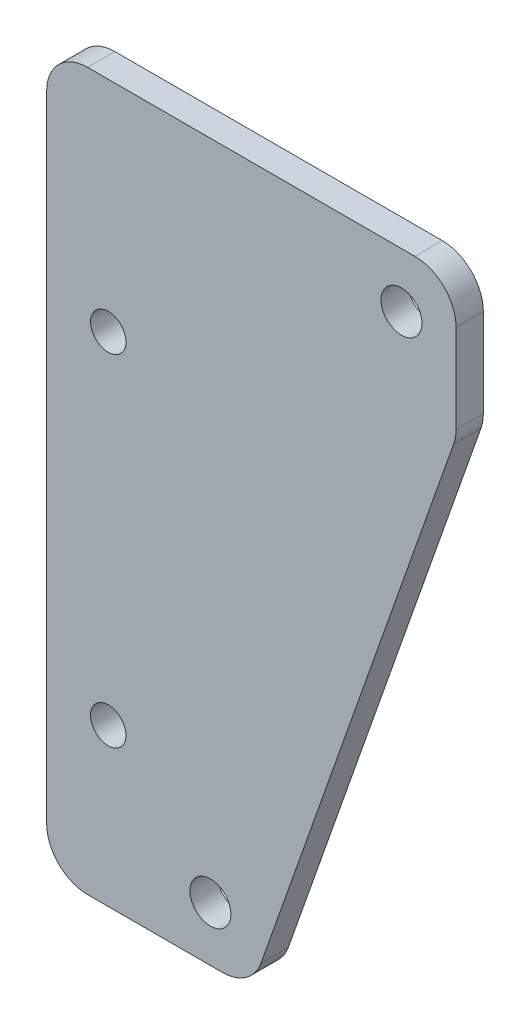
SolidWorks part; units mm, degrees
material "环氧板3240"
ref_plane "前视基准面" through (0, 0, 0) normal (0, 0, 1) x (1, 0, 0)
ref_plane "上视基准面" through (0, 0, 0) normal (0, 1, 0) x (1, 0, 0)
ref_plane "右视基准面" through (0, 0, 0) normal (1, 0, 0) x (0, 0, -1)
other "Configuration Table"
sketch "草图1" plane through (0, 0, 0) normal (0, 0, 1) x (1, 0, 0)
  line L0 (30, 0) -> (0, 0)
  line L1 (0, 0) -> (0, -52.5)
  line L2 (0, -52.5) -> (15, -52.5)
  line L3 (15, -52.5) -> (30, -10)
  line L4 (30, -10) -> (30, 0)
  circle A0 centre (26, -4) radius 1.5
  circle A1 centre (4, -18) radius 1.25 construction
  circle A2 centre (3.5, -41) radius 1.25 construction
  circle A3 centre (12, -48.5) radius 1.5
  circle A8 centre (4.515, -41) radius 1.3
  circle A9 centre (4.515, -16.0289) radius 1.3
  point P15 (4.515, -16.0289)
  point P18 (0, 0)
  point P20 (3.5, -40.9907)
  point P21 (4.515, -41)
  dimension "D4" = 4
  dimension "D5" = 3
  dimension "D8" = 14
  dimension "D9" = 22
  dimension "D10" = 23
  dimension "D11" = 0.5
  dimension "D12" = 2.5
  dimension "D13" = 3
  dimension "D15" = 44.5
  dimension "D6" = 4
  dimension "D14" = 14
  dimension "D17" = 2.6
  dimension "D1" = 30
  dimension "D2" = 2.75
  dimension "D3" = 4
  dimension "D7" = 10
  dimension "D16" = 15
extrude "凸台-拉伸1" add sketch "草图1" along normal blind 2
fillet "圆角1" radius 3 5 edges at (30, -10, 1) (30, 0, 1) (0, 0, 1) (0, -52.5, 1) (15, -52.5, 1)
